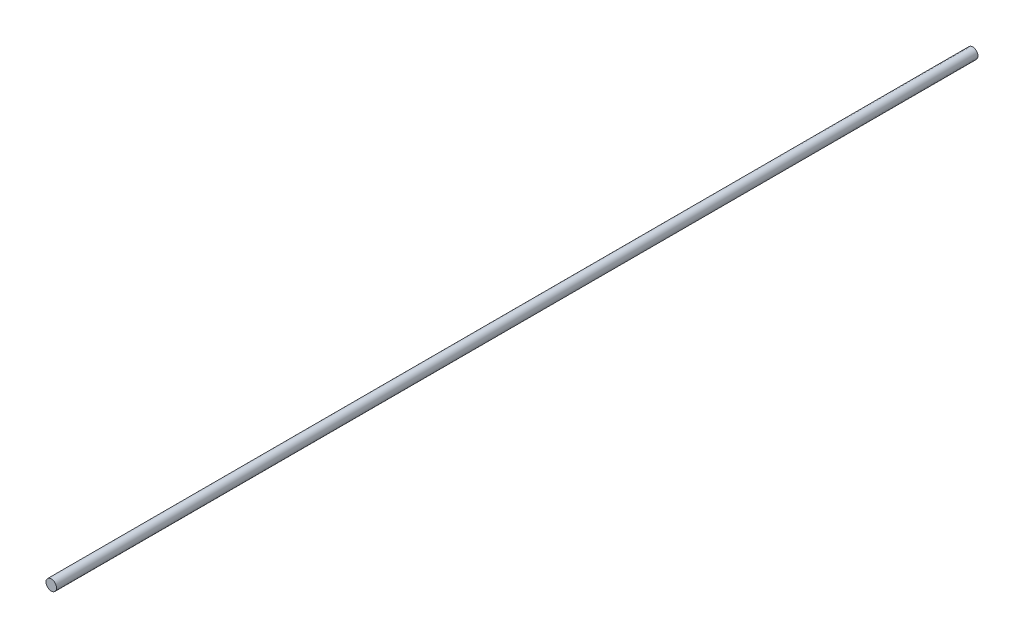
SolidWorks part; units mm, degrees
material "Brass"
ref_plane "Front Plane" through (0, 0, 0) normal (0, 0, 1) x (1, 0, 0)
ref_plane "Top Plane" through (0, 0, 0) normal (0, 1, 0) x (1, 0, 0)
ref_plane "Right Plane" through (0, 0, 0) normal (1, 0, 0) x (0, 0, -1)
sketch "Sketch1" plane through (0, 0, 0) normal (0, 0, 1) x (1, 0, 0)
  circle A0 centre (0, 0) radius 0.254
  dimension "D1" = 0.508
extrude "Boss-Extrude1" add sketch "Sketch1" along normal mid plane 44.45
